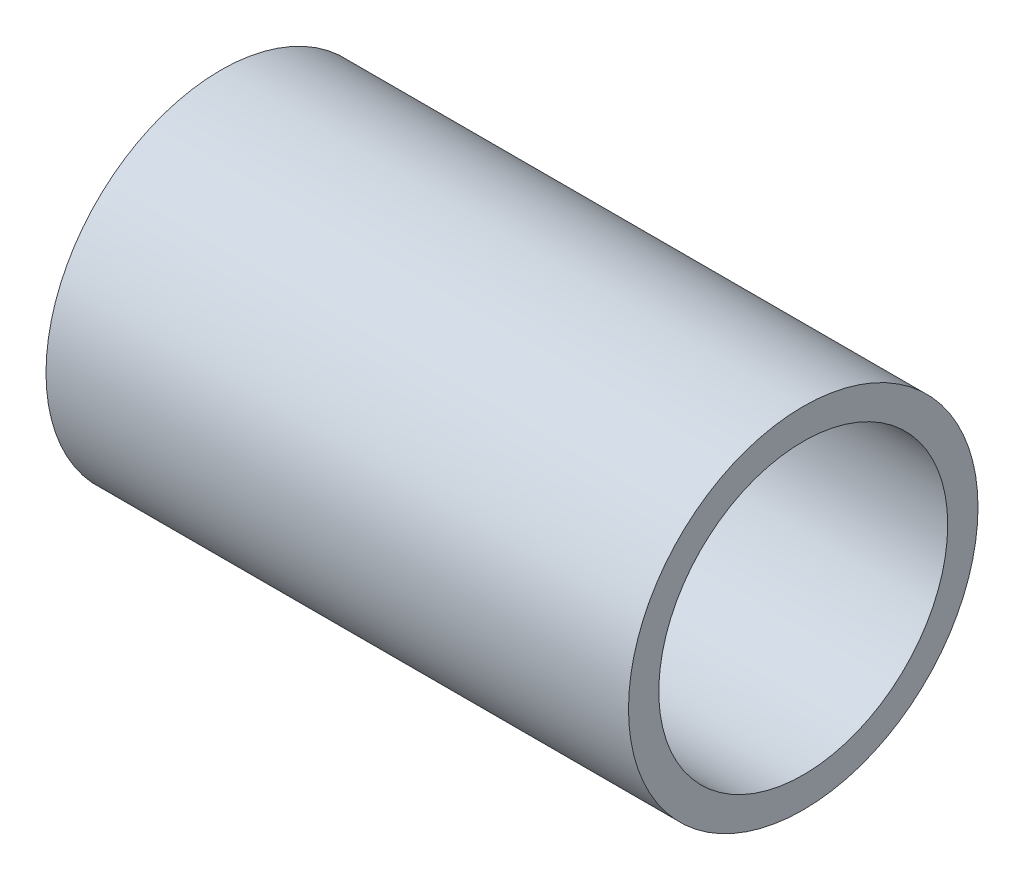
SolidWorks part; units mm, degrees
material "6061 Alloy"
ref_plane "Front Plane" through (0, 0, 0) normal (0, 0, 1) x (1, 0, 0)
ref_plane "Top Plane" through (0, 0, 0) normal (0, 1, 0) x (1, 0, 0)
ref_plane "Right Plane" through (0, 0, 0) normal (1, 0, 0) x (0, 0, -1)
sketch "Sketch1" plane through (0, 0, 0) normal (1, 0, 0) x (0, 0, -1)
  circle A0 centre (0, 0) radius 9.525
  circle A1 centre (0, 0) radius 7.874
  dimension "D1" = 19.05
  dimension "D2" = 15.748
extrude "Boss-Extrude1" add sketch "Sketch1" along normal mid plane 31.75
